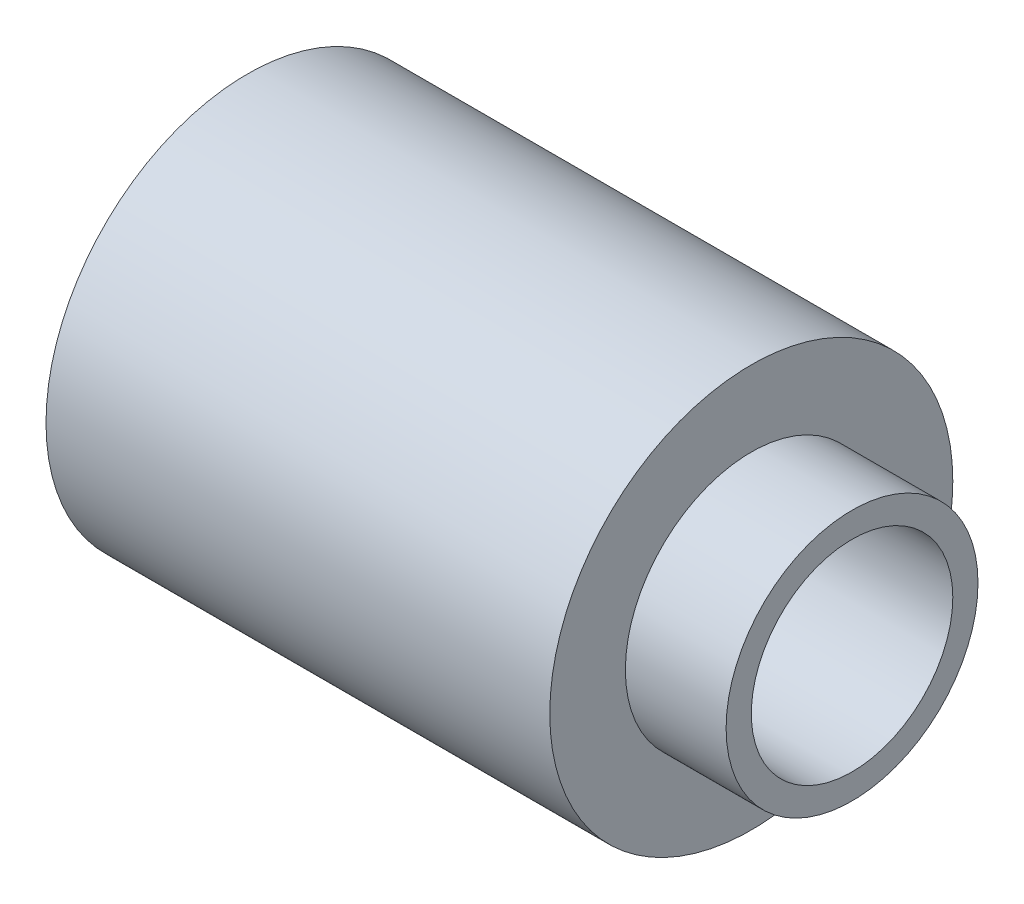
SolidWorks part; units mm, degrees
ref_plane "Front Plane" through (0, 0, 0) normal (0, 0, 1) x (1, 0, 0)
ref_plane "Top Plane" through (0, 0, 0) normal (0, 1, 0) x (1, 0, 0)
ref_plane "Right Plane" through (0, 0, 0) normal (1, 0, 0) x (0, 0, -1)
sketch "Sketch1" plane through (0, 0, 0) normal (1, 0, 0) x (0, 0, -1)
  circle A0 centre (0, 0) radius 4
  circle A1 centre (0, 0) radius 2
  dimension "D1" = 8
  dimension "D2" = 4
extrude "Boss-Extrude1" add sketch "Sketch1" along normal blind 10
sketch "Sketch2" plane through (10, 0, 0) normal (1, 0, 0) x (0, 0, -1)
  circle A0 centre (0, 0) radius 2 construction
  circle A1 centre (0, 0) radius 2
  circle A2 centre (0, 0) radius 2.5
  dimension "D1" = 0.5
extrude "Boss-Extrude2" add sketch "Sketch2" along normal blind 2
